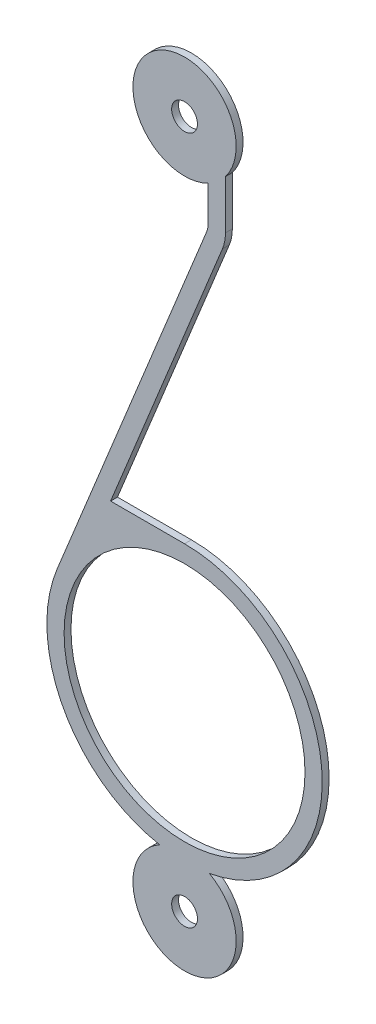
SolidWorks part; units mm, degrees
material "3.0517 (EN-AW 3003)"
ref_plane "Front Plane" through (0, 0, 0) normal (0, 0, 1) x (1, 0, 0)
ref_plane "Top Plane" through (0, 0, 0) normal (0, 1, 0) x (1, 0, 0)
ref_plane "Right Plane" through (0, 0, 0) normal (1, 0, 0) x (0, 0, -1)
sketch "Sketch1" plane through (0, 0, 0) normal (0, 0, 1) x (1, 0, 0)
  line L0 (0, 10) -> (0, -10) construction
  line L1 (-4, -8.75) -> (4, -8.75) construction
  line L2 (-4, -8.75) -> (-4, -4.75) construction
  line L3 (4, -8.75) -> (4, -4.75) construction
  line L4 (0.6875, 10) -> (0.6875, 7.6668) construction
  line L5 (0.6875, 10) -> (1.1875, 10) construction
  line L6 (1.1875, 10) -> (1.1875, 7.6668) construction
  line L7 (0.375, 10) -> (0.6875, 10) construction
  line L8 (0.6366, 7.4073) -> (-3.704, -3.24)
  line L9 (1.0996, 7.2185) -> (-2.149, -0.75)
  line L10 (1.1875, 7.6668) -> (1.1875, 9.0836)
  line L11 (0.6875, 7.6668) -> (0.6875, 8.6668)
  line L12 (1.1875, 10) -> (1.5, 10) construction
  line L13 (0, -0.75) -> (-2.149, -0.75)
  arc A0 (1.1875, 9.0836) -> (0.6875, 8.6668) centre (0, 10) ccw
  circle A1 centre (0, 10) radius 0.375
  arc A2 (-0.7208, -8.6845) -> (0.7208, -8.6845) centre (0, -10) ccw
  circle A3 centre (0, -10) radius 0.375
  arc A4 (-3.704, -3.24) -> (-0.7208, -8.6845) centre (0, -4.75) ccw
  arc A5 (0.6875, 7.6668) -> (0.6366, 7.4073) centre (0, 7.6668) cw
  arc A6 (1.1875, 7.6668) -> (1.0996, 7.2185) centre (0, 7.6668) cw
  circle A7 centre (0, -4.75) radius 3.5
  circle A8 centre (0, -4.75) radius 4 construction
  arc A9 (0.7208, -8.6845) -> (0, -0.75) centre (0, -4.75) ccw
  point P9 (0, -8.75)
  dimension "D2" = 3
  dimension "D3" = 0.75
  dimension "D4" = 8
  dimension "D6" = 0.5
  dimension "D7" = 0.5
  dimension "D1" = 20
  dimension "D5" = 1.25
  dimension "D8" = 1
extrude "Boss-Extrude1" add sketch "Sketch1" along normal mid plane 0.2
sketch "Sketch2" plane through (0, 0, 0) normal (0, 0, 1) x (1, 0, 0)
  line L5 (0.4375, 8.5652) -> (1.4375, 9.5715)
  line L10 (0, -0.5) -> (-1.7771, -0.5)
  line L11 (-1.7771, -0.5) -> (1.3311, 7.1242)
  line L12 (1.4375, 7.6668) -> (1.4375, 9.002)
  line L13 (0.4375, 8.3056) -> (0.4375, 7.6668)
  line L14 (0.4051, 7.5017) -> (-3.9355, -3.1456)
  line L15 (0, -0.5) -> (-1.7771, -0.5)
  line L16 (-1.7771, -0.5) -> (1.3311, 7.1242)
  line L17 (1.4375, 7.6668) -> (1.4375, 9.5715)
  line L18 (0.4375, 8.5652) -> (0.4375, 7.6668)
  line L19 (0.4051, 7.5017) -> (-3.9355, -3.1456)
  arc A7 (1.1875, 9.0836) -> (0.6875, 8.6668) centre (0, 10) ccw construction
  circle A8 centre (0, -4.75) radius 3.25
  circle A9 centre (0, -4.75) radius 3.25
  arc A10 (1.1875, 9.0836) -> (0.6875, 8.6668) centre (0, 10) ccw construction
  arc A12 (1.2771, -8.8036) -> (0, -0.5) centre (0, -4.75) ccw
  arc A13 (1.3311, 7.1242) -> (1.4375, 7.6668) centre (0, 7.6668) ccw
  arc A14 (1.4375, 9.002) -> (0.4375, 8.3056) centre (0, 10) ccw
  arc A15 (0.4051, 7.5017) -> (0.4375, 7.6668) centre (0, 7.6668) ccw
  arc A16 (-3.9355, -3.1456) -> (-1.2771, -8.8036) centre (0, -4.75) ccw
  arc A17 (-1.2771, -8.8036) -> (1.2771, -8.8036) centre (0, -10) ccw
  arc A18 (0, -9) -> (0, -0.5) centre (0, -4.75) ccw
  arc A19 (1.3311, 7.1242) -> (1.4375, 7.6668) centre (0, 7.6668) ccw
  arc A21 (0.4051, 7.5017) -> (0.4375, 7.6668) centre (0, 7.6668) ccw
  arc A22 (-3.9355, -3.1456) -> (0, -9) centre (0, -4.75) ccw
  dimension "D1" = 0.25
  dimension "D2" = 0.25
extrude "Boss-Extrude2" [suppressed] add sketch "Sketch2" along normal mid plane 0.6
